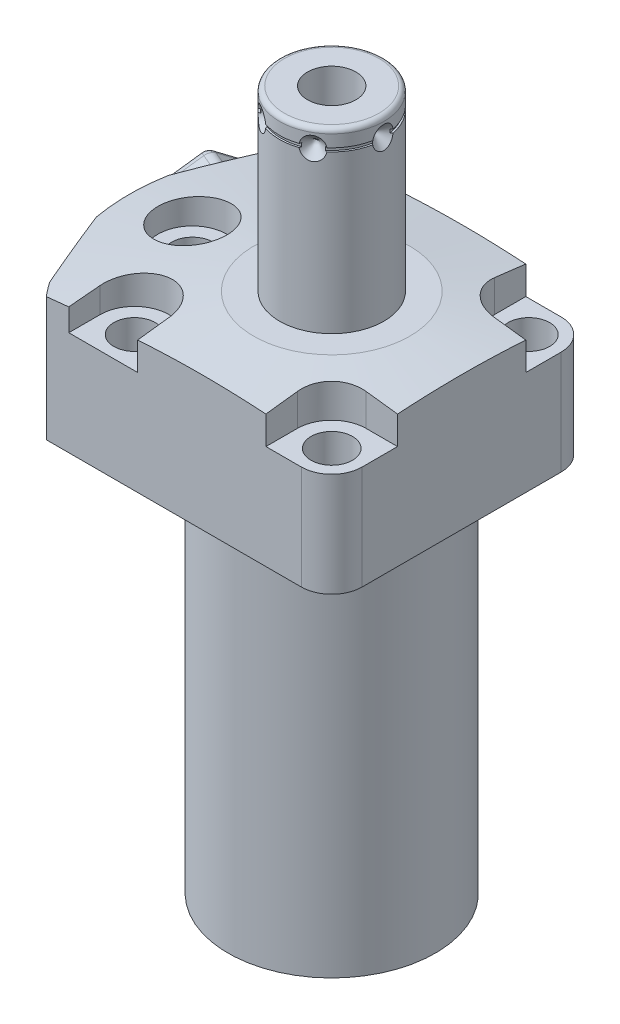
SolidWorks part; units mm, degrees
material "Alloy Steel"
ref_plane "Front Plane" through (0, 0, 0) normal (0, 0, 1) x (1, 0, 0)
ref_plane "Top Plane" through (0, 0, 0) normal (0, 1, 0) x (1, 0, 0)
ref_plane "Right Plane" through (0, 0, 0) normal (1, 0, 0) x (0, 0, -1)
sketch "S2D0002" plane through (0, 0, 0) normal (0, 0, 1) x (1, 0, 0)
  line L0 (-43.18, 0) -> (-43.18, 30.1498)
  line L1 (-43.18, 30.1498) -> (0, 30.1498)
  line L2 (0, 30.1498) -> (0, -80.9752)
  line L3 (0, -80.9752) -> (-22.098, -80.9752)
  line L4 (-22.098, -80.9752) -> (-22.098, 0)
  line L5 (-22.098, 0) -> (-43.18, 0)
  line L6 (0, -3.4925) -> (0, 73.3425) construction
  dimension "D1" = 111.125
  dimension "D2" = 44.196
  dimension "D3" = 86.36
  dimension "D4" = 80.9752
revolve "Revolve1" add sketch "S2D0002" angle 360 about L6
sketch "S2D0001" plane through (0, 0, 0) normal (0, -1, 0) x (1, 0, 0)
  line L0 (-33.136, -27.686) -> (33.136, -27.686)
  line L2 (33.136, 27.686) -> (-33.136, 27.686)
  line L3 (0, 0) -> (59.5614, 0) construction
  arc A0 (-33.136, -27.686) -> (33.136, -27.686) centre (0, 0) ccw
  circle A1 centre (0, 0) radius 43.18
  arc A2 (33.136, 27.686) -> (-33.136, 27.686) centre (0, 0) ccw
  point P4 (25.1041, 0)
  dimension "D1" = 55.372
  dimension "D2" = 0
extrude "Cut-Extrude1" cut sketch "S2D0001" against normal blind 32.9946
sketch "Sketch3" plane through (0, 30.1498, 0) normal (0, -1, 0) x (-1, 0, 0)
  line L0 (21.3317, 58.747) -> (45.6655, 0)
  line L1 (45.6655, 0) -> (21.3317, -58.747)
  line L2 (-32.7616, -13.5703) -> (61.25, 25.3706) construction
  line L3 (0, 0) -> (47.9453, 0) construction
  arc A0 (21.3317, -58.747) -> (21.3317, 58.747) centre (0, 0) ccw
  dimension "D3" = 125
  dimension "D1" = 22.5
  dimension "D2" = 42.1894
extrude "Cut-Extrude2" cut sketch "Sketch3" along normal up to surface (30.1498 mm away) up to face at (0, 0, -22.098)
sketch "Sketch4" plane through (0, 0, 0) normal (0, -1, 0) x (1, 0, 0)
  line L0 (27.686, -33.136) -> (27.686, 33.136)
  line L1 (-33.136, 27.686) -> (33.136, 27.686) construction
  arc A0 (27.686, -33.136) -> (27.686, 33.136) centre (0, 0) ccw
  arc A1 (33.136, -27.686) -> (33.136, 27.686) centre (0, 0) ccw construction
  dimension "D1" = 27.686
extrude "Cut-Extrude3" cut sketch "Sketch4" against normal blind 32.9946
fillet "Fillet1" radius 6.477 2 edges at (27.686, 15.0749, 27.686) (27.686, 15.0749, -27.686)
sketch "Sketch5" plane through (0, 30.1498, 0) normal (0, 1, 0) x (-1, 0, 0)
  line L0 (0, 0) -> (-37.3124, 0) construction
  line L1 (-27.686, 21.209) -> (-27.686, -21.209) construction
  line L2 (-21.209, -27.686) -> (33.136, -27.686) construction
  line L3 (-27.686, -13.6652) -> (-27.686, -27.686)
  line L4 (-27.686, -27.686) -> (-13.6652, -27.686)
  line L5 (-27.686, -13.6652) -> (-21.0058, -13.6652)
  line L6 (-13.6652, -21.0058) -> (-13.6652, -27.686)
  line L7 (-13.6652, 21.0058) -> (-13.6652, 27.686)
  line L8 (-27.686, 13.6652) -> (-21.0058, 13.6652)
  line L9 (0, 0.7832) -> (0, 0) construction
  line L10 (0, 0) -> (47.8281, 0) construction
  line L11 (-27.686, 27.686) -> (-13.6652, 27.686)
  line L12 (-27.686, 13.6652) -> (-27.686, 27.686)
  line L13 (0, 0) -> (0, 43.3168) construction
  line L14 (33.136, 27.686) -> (-21.209, 27.686) construction
  line L15 (13.6652, 27.686) -> (28.3464, 27.686)
  line L16 (13.6652, 27.686) -> (13.6652, 21.0058)
  line L17 (13.6652, -27.686) -> (13.6652, -21.0058)
  line L18 (28.3464, 27.686) -> (28.3464, 21.0058)
  line L19 (28.3464, -27.686) -> (28.3464, -21.0058)
  line L20 (13.6652, -27.686) -> (28.3464, -27.686)
  arc A0 (-13.6652, -21.0058) -> (-21.0058, -13.6652) centre (-21.0058, -21.0058) ccw
  arc A1 (-13.6652, 21.0058) -> (-21.0058, 13.6652) centre (-21.0058, 21.0058) cw
  arc A2 (28.3464, 21.0058) -> (13.6652, 21.0058) centre (21.0058, 21.0058) cw
  arc A3 (28.3464, -21.0058) -> (13.6652, -21.0058) centre (21.0058, -21.0058) ccw
  dimension "D3" = 21.0058
  dimension "D1" = 7.3406
  dimension "D2" = 21.0058
  dimension "D4" = 21.0058
extrude "Cut-Extrude4" cut sketch "Sketch5" against normal blind 8.001
sketch "S2D0003" plane through (0, 0, 0) normal (0, 0, 1) x (1, 0, 0)
  line L0 (-16.637, 30.1498) -> (-86.637, 20.3119)
  line L1 (0, 12.958) -> (0, 26.6311) construction
  line L2 (-16.637, 30.1498) -> (-86.637, 30.1498)
  line L3 (-86.637, 30.1498) -> (-86.637, 20.3119)
  line L4 (-33.136, 30.1498) -> (-28.3464, 30.1498) construction
  dimension "D1" = 33.274
  dimension "D2" = 8
  dimension "D3" = 70
revolve "Cut-Revolve1" cut sketch "S2D0003" angle 360 about L1
ref_plane "Plane20" through (0, 14.5034, 0) normal (0, -1, 0) x (1, 0, 0)
sketch "Sketch7" plane through (0, 14.5034, 0) normal (0, -1, 0) x (1, 0, 0)
  line L0 (-41.1733, -10.1813) -> (-42.8571, -6.1163)
  line L1 (-41.1733, -10.1813) -> (-41.0456, -10.1577)
  line L2 (-41.0456, -10.1577) -> (-40.5499, -10.363)
  line L3 (-40.5499, -10.363) -> (-27.9234, -5.133)
  line L4 (-27.9234, -5.133) -> (-25.6489, -10.6241)
  line L5 (-25.6489, -10.6241) -> (-38.9779, -16.1452)
  line L6 (0, 0) -> (22.0051, 9.1148) construction
  line L7 (-42.4971, -7.6492) -> (-35.4588, -24.6412) construction
  line L8 (-42.8571, -6.1163) -> (-43.0918, -6.2135)
  line L9 (-43.0918, -6.2135) -> (-38.9779, -16.1452)
  line L11 (-42.4971, -7.6492) -> (-35.4588, -24.6412) construction
  dimension "D1" = 14.1732
  dimension "D2" = 11.8872
  dimension "D3" = 45
  dimension "D4" = 0.254
  dimension "D5" = 0.5064
  dimension "D6" = 12.7
  dimension "D7" = 21.5
  dimension "D8" = 78
revolve "Cut-Revolve2" cut sketch "Sketch7" angle 360 about L6
ref_plane "Plane21" through (0, 0, -11.8364) normal (0, 0, 1) x (1, 0, 0)
sketch "Sketch9" plane through (0, 0, -11.8364) normal (0, 0, 1) x (1, 0, 0)
  line L0 (-31.8262, 1.5) -> (-33.575, 1.5)
  line L1 (-31.8262, 1.5) -> (-31.8262, 4.4972)
  line L2 (-31.8262, 4.4972) -> (-29.8196, 4.4972)
  line L3 (-29.8196, 4.4972) -> (-29.8196, 12.0664)
  line L4 (-29.8196, 12.0664) -> (-28.575, 12.0664)
  line L5 (-28.575, 12.0664) -> (-28.575, 0)
  line L6 (-28.575, -17.8934) -> (-28.575, 0.5283) construction
  line L7 (-33.136, 0) -> (21.209, 0) construction
  line L8 (-33.575, 0) -> (-33.575, 1.5)
  line L9 (-35.4588, 0) -> (-42.4971, 0) construction
  line L10 (-33.575, 0) -> (-28.575, 0)
  dimension "D1" = 7.5692
  dimension "D2" = 2.9972
  dimension "D3" = 28.575
  dimension "D4" = 2.4892
  dimension "D5" = 6.5024
  dimension "D6" = 10
  dimension "D7" = 1.5
revolve "Cut-Revolve4" cut sketch "Sketch9" angle 360 about L6
sketch "Sketch11" plane through (0, 4.4972, 0) normal (0, -1, 0) x (1, 0, 0)
  circle A0 centre (-28.575, -11.8364) radius 2.7432
  circle A1 centre (-28.575, -11.8364) radius 3.2512 construction
  dimension "D1" = 5.4864
extrude "Extrude1" add sketch "Sketch11" along normal blind 2.9972
sketch "Sketch12" plane through (0, 1.5, 0) normal (0, -1, 0) x (1, 0, 0)
  line L7 (-27.3304, -12.555) -> (-27.3304, -11.1178)
  line L8 (-27.3304, -11.1178) -> (-28.575, -10.3993)
  line L9 (-28.575, -10.3993) -> (-29.8196, -11.1178)
  line L10 (-29.8196, -11.1178) -> (-29.8196, -12.555)
  line L11 (-29.8196, -12.555) -> (-28.575, -13.2735)
  line L12 (-28.575, -13.2735) -> (-27.3304, -12.555)
  circle A0 centre (-28.575, -11.8364) radius 1.2446 construction
  circle A1 centre (-28.575, -11.8364) radius 2.7432 construction
  dimension "D2" = 2.4892
extrude "Cut-Extrude5" cut sketch "Sketch12" against normal blind 1.27
chamfer "Chamfer1" distance 0.254 angle 45 1 edges at (-28.575, 1.5, -14.5796)
mirror "Mirror2" about plane through (0, 0, 0) normal (0, 0, 1) of "Chamfer1", "Cut-Extrude5", "Extrude1", "Cut-Revolve4", "Cut-Revolve2"
sketch "Sketch16" plane through (-18.1864, 0, -11.8364) normal (0, 0, -1) x (-1, 0, 0)
  line L0 (10.3886, -0.4101) -> (10.3886, 1.5457) construction
  line L1 (5.3886, 1.5) -> (15.3886, 1.5) construction
  line L2 (7.1374, 4.4972) -> (7.1374, 1.5) construction
  line L3 (13.6398, 1.5) -> (13.6398, 4.4972) construction
  circle A0 centre (14.3886, 0.5) radius 1
  dimension "D2" = 2
  dimension "D1" = 8
  dimension "D3" = 1
revolve "Revolve3" add sketch "Sketch16" angle 360 about L0
mirror "Mirror3" about plane through (0, 0, 0) normal (0, 0, 1) of bodies 123 141
sketch "Sketch17" plane through (0, 0, 0) normal (1, 0, 0) x (0, 0, -1)
  line L0 (0, 30.1498) -> (-11.1125, 30.1498)
  line L1 (-11.1125, 30.1498) -> (-11.1125, 67.018)
  line L2 (-10.0965, 68.034) -> (0, 68.034)
  line L3 (0, 68.034) -> (0, 30.1498)
  line L4 (0, 24.9961) -> (0, 47.2925) construction
  line L5 (16.637, 30.1498) -> (-16.637, 30.1498) construction
  line L6 (-24.6412, 0) -> (-7.6492, 0) construction
  arc A0 (-10.0965, 68.034) -> (-11.1125, 67.018) centre (-10.0965, 67.018) ccw
  dimension "D2" = 1.016
  dimension "D1" = 22.225
  dimension "D3" = 68.034
revolve "Revolve4" add sketch "Sketch17" angle 360 about L4
sketch "Sketch18" plane through (0, 0, 0) normal (0, 0, 1) x (1, 0, 0)
  line L0 (5.1562, 68.034) -> (5.1562, 51.016)
  line L1 (5.1562, 51.016) -> (0, 47.9178)
  line L2 (5.1562, 68.034) -> (0, 68.034)
  line L3 (0, 68.034) -> (0, 47.9178)
  line L4 (0, -20.476) -> (0, 0.5839) construction
  line L5 (10.0965, 68.034) -> (-10.0965, 68.034) construction
  dimension "D1" = 17.018
  dimension "D2" = 10.3124
  dimension "D3" = 59
revolve "Cut-Revolve7" cut sketch "Sketch18" angle 360 about L4
sketch "Sketch19" plane through (-52.2568, 0, 16.5766) normal (-0.9239, 0, -0.3827) x (-0.3827, 0, 0.9239)
  circle A0 centre (-35.3126, 14.5034) radius 8.5
  circle A1 centre (-35.3126, 14.5034) radius 5.9436 construction
  dimension "D1" = 17
extrude "Extrude3" add sketch "Sketch19" along normal blind 1
sketch "Sketch20" plane through (0, 0, 0) normal (0, 0, 1) x (1, 0, 0)
  line L3 (0, 64.0716) -> (4.3349, 64.0716) construction
  line L4 (-11.1125, 67.018) -> (-11.1125, 30.1498) construction
  line L5 (10.0965, 68.034) -> (-10.0965, 68.034) construction
  line L6 (-11.1125, 61.6586) -> (-11.1125, 64.0716)
  line L7 (-11.1125, 64.0716) -> (-8.6995, 64.0716)
  line L8 (-8.6995, 64.0716) -> (-11.1125, 61.6586)
  dimension "D1" = 3.9624
  dimension "D2" = 4.826
  dimension "D4" = 45
revolve "Cut-Revolve8" cut sketch "Sketch20" angle 360 about L3
sketch "Sketch22" plane through (0, 0, 0) normal (1, 0, 0) x (0, 0, -1)
  line L0 (11.1125, 64.453) -> (10.7315, 64.453)
  line L1 (10.7315, 64.453) -> (10.7315, 63.691)
  line L2 (10.7315, 63.691) -> (11.1125, 63.691)
  line L3 (11.1125, 63.691) -> (11.1125, 64.453)
  line L4 (0, 41.8979) -> (0, 49.0468) construction
  line L5 (5.1562, 68.034) -> (-5.1562, 68.034) construction
  line L6 (10.0965, 68.034) -> (-10.0965, 68.034) construction
  line L7 (11.1125, 30.1498) -> (11.1125, 67.018) construction
  dimension "D1" = 0.762
  dimension "D2" = 0.381
  dimension "D3" = 3.581
revolve "Cut-Revolve6" cut sketch "Sketch22" angle 360 about L4
hole_wizard "Hole1" positions "Sketch24" profile "Sketch23" legacy end condition up to next
sketch "Sketch24" plane through (0, 30.1498, 0) normal (0, 1, 0) x (-1, 0, 0)
  arc A0 (-13.6652, -21.0058) -> (-21.0058, -13.6652) centre (-21.0058, -21.0058) ccw construction
  arc A1 (-21.0058, 13.6652) -> (-13.6652, 21.0058) centre (-21.0058, 21.0058) ccw construction
  point P0 (29.6926, 0)
  point P1 (-21.0058, 21.0058)
  point P3 (-21.0058, -21.0058)
  point P15 (21.0058, 21.0058)
  point P18 (21.0058, -21.0058)
  dimension "D1" = 29.6926
sketch "Sketch23" plane through (-29.6926, 30.1498, 0) normal (1, 0, 0) x (0, 0, 1)
  line L0 (0, 0) -> (0, 30.1498)
  line L1 (0, 30.1498) -> (4.4196, 30.1498)
  line L2 (4.4196, 30.1498) -> (4.4196, 8.001)
  line L3 (4.4196, 8.001) -> (7.3406, 8.001)
  line L4 (7.3406, 8.001) -> (7.3406, 0)
  line L5 (7.3406, 0) -> (0, 0)
  line L6 (0, 110) -> (0, -10) construction
  dimension "Diameter" = 8.8392
  dimension "Depth" = 30.1498
  dimension "C-Bore Diameter" = 14.6812
  dimension "C-Bore Depth" = 8.001
sketch "Sketch25" plane through (0, -80.9752, 0) normal (0, -1, 0) x (1, 0, 0)
  circle A0 centre (0, 0) radius 11.3665
  dimension "D1" = 22.733
extrude "Cut-Extrude7" cut sketch "Sketch25" against normal blind 1.524
sketch "Sketch27" plane through (-39.6671, 0, -16.4307) normal (-0.9239, 0, -0.3827) x (-0.3827, 0, 0.9239)
  line L1 (8.3998, 19.5804) -> (-0.1969, 24.3164)
  line L2 (-0.1969, 24.3164) -> (-8.5967, 19.2394)
  line L3 (-8.5967, 19.2394) -> (-8.3998, 9.4264)
  line L4 (-8.3998, 9.4264) -> (0.1969, 4.6904)
  line L5 (0.1969, 4.6904) -> (8.5967, 9.7674)
  line L6 (8.5967, 9.7674) -> (8.3998, 19.5804)
  circle A0 centre (0, 14.5034) radius 8.5 construction
  dimension "D1" = 17
extrude "Extrude4" add sketch "Sketch27" along normal blind 7.471
fillet "Fillet2" radius 2 12 edges at (-39.8285, 19.2394, -25.8025) (-43.3173, 14.3329, -27.1411) (-44.9999, 7.0584, -23.0789) (-39.9038, 9.4264, -25.6206) (-43.1936, 4.6904, -17.6782) (-48.252, 7.2289, -15.2275) (-46.4081, 9.7674, -9.9178) (-46.3328, 19.5804, -10.0998) (-49.8216, 14.6739, -11.4383) (-48.139, 21.9484, -15.5004) (-43.0429, 24.3164, -18.0421) (-44.8868, 21.7779, -23.3518)
pattern_circular "CirPattern1" count 6 over 360 about axis through (0, -3.4925, 0) along (0, 1, 0) of "Cut-Revolve8"
